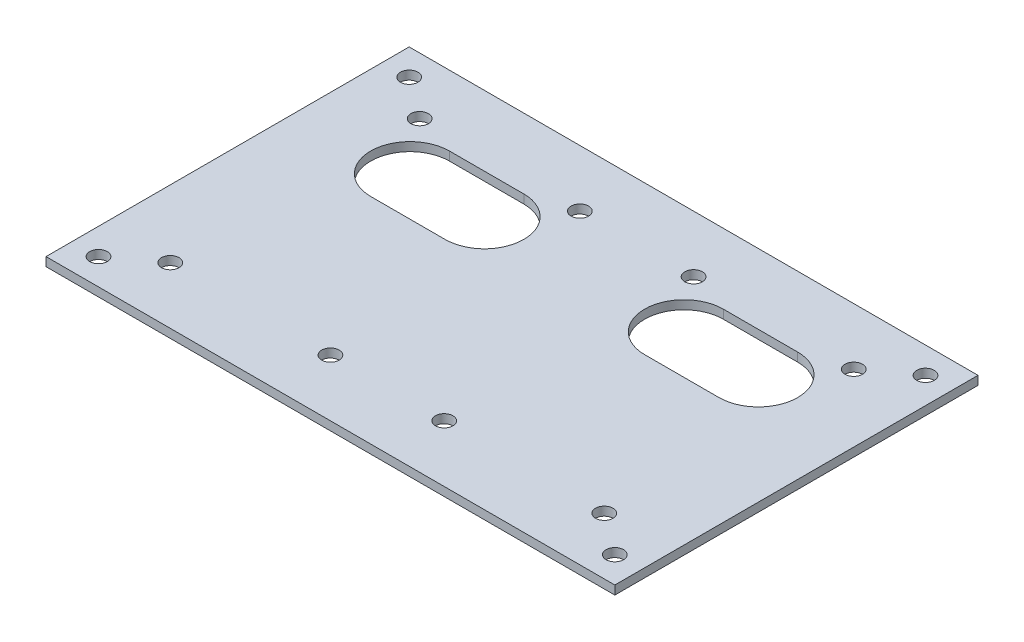
SolidWorks part; units mm, degrees
ref_plane "Front Plane" through (0, 0, 0) normal (0, 0, 1) x (1, 0, 0)
ref_plane "Top Plane" through (0, 0, 0) normal (0, 1, 0) x (1, 0, 0)
ref_plane "Right Plane" through (0, 0, 0) normal (1, 0, 0) x (0, 0, -1)
sketch "Sketch1" plane through (0, 0, 0) normal (0, 1, 0) x (1, 0, 0)
  line L0 (0, 53.99) -> (0, -62.5646) construction
  line L1 (10, 31.5) -> (52.6, 31.5) construction
  line L2 (10, 31.5) -> (10, -31.5) construction
  line L3 (10, -31.5) -> (52.6, -31.5) construction
  line L4 (52.6, 31.5) -> (52.6, -31.5) construction
  line L5 (10, 31.5) -> (52.6, -31.5) construction
  line L6 (10, -31.5) -> (52.6, 31.5) construction
  line L7 (13, 28.5) -> (49.6, 28.5) construction
  line L8 (13, 28.5) -> (13, -28.5) construction
  line L9 (13, -28.5) -> (49.6, -28.5) construction
  line L10 (49.6, 28.5) -> (49.6, -28.5) construction
  line L11 (13, 28.5) -> (49.6, -28.5) construction
  line L12 (13, -28.5) -> (49.6, 28.5) construction
  line L13 (-13, -28.5) -> (-49.6, 28.5) construction
  line L14 (-13, 28.5) -> (-49.6, -28.5) construction
  line L15 (-49.6, 28.5) -> (-49.6, -28.5) construction
  line L16 (-13, -28.5) -> (-49.6, -28.5) construction
  line L17 (-13, 28.5) -> (-13, -28.5) construction
  line L18 (-13, 28.5) -> (-49.6, 28.5) construction
  line L19 (-10, -31.5) -> (-52.6, 31.5) construction
  line L20 (-10, 31.5) -> (-52.6, -31.5) construction
  line L21 (-52.6, 31.5) -> (-52.6, -31.5) construction
  line L22 (-10, -31.5) -> (-52.6, -31.5) construction
  line L23 (-10, 31.5) -> (-10, -31.5) construction
  line L24 (-10, 31.5) -> (-52.6, 31.5) construction
  line L25 (-59, 35.5) -> (59, 35.5) construction
  line L26 (-65, 41.5) -> (65, 41.5)
  line L27 (-65, 41.5) -> (-65, -41.5)
  line L28 (-65, -41.5) -> (65, -41.5)
  line L29 (65, 41.5) -> (65, -41.5)
  line L30 (-65, 41.5) -> (65, -41.5) construction
  line L31 (-65, -41.5) -> (65, 41.5) construction
  line L32 (59, 35.5) -> (59, -35.5) construction
  line L33 (-59, -35.5) -> (59, -35.5) construction
  line L34 (-59, 35.5) -> (-59, -35.5) construction
  line L35 (31.3, 31.5) -> (31.3, -31.5) construction
  line L36 (22.8, 16.5) -> (39.8, 16.5) construction
  line L37 (22.8, 16.5) -> (39.8, 16.5) construction
  line L38 (22.8, 25.5) -> (39.8, 25.5)
  line L39 (22.8, 7.5) -> (39.8, 7.5)
  line L40 (-22.8, 16.5) -> (-39.8, 16.5) construction
  line L41 (-22.8, 25.5) -> (-39.8, 25.5)
  line L42 (-22.8, 7.5) -> (-39.8, 7.5)
  circle A0 centre (13, 28.5) radius 2
  circle A1 centre (49.6, 28.5) radius 2
  circle A2 centre (49.6, -28.5) radius 2
  circle A3 centre (13, -28.5) radius 2
  circle A4 centre (-13, -28.5) radius 2
  circle A5 centre (-49.6, -28.5) radius 2
  circle A6 centre (-49.6, 28.5) radius 2
  circle A7 centre (-13, 28.5) radius 2
  circle A8 centre (-59, 35.5) radius 2
  circle A9 centre (59, 35.5) radius 2
  circle A10 centre (59, -35.5) radius 2
  circle A11 centre (-59, -35.5) radius 2
  arc A12 (22.8, 25.5) -> (22.8, 7.5) centre (22.8, 16.5) ccw
  arc A13 (39.8, 7.5) -> (39.8, 25.5) centre (39.8, 16.5) ccw
  arc A14 (-22.8, 25.5) -> (-22.8, 7.5) centre (-22.8, 16.5) cw
  arc A15 (-39.8, 7.5) -> (-39.8, 25.5) centre (-39.8, 16.5) cw
  point P0 (31.3, 0)
  point P5 (31.3, 0)
  point P30 (-31.3, 0)
  point P31 (0, 0)
  point P43 (31.3, 16.5)
  point P46 (31.3, 0)
  point P49 (31.3, 16.5)
  point P54 (13.8, 16.5)
  point P57 (-31.3, 16.5)
  dimension "D5" = 4
  dimension "D10" = 4
  dimension "D1" = 42.6
  dimension "D2" = 63
  dimension "D3" = 3
  dimension "D4" = 3
  dimension "D6" = 10
  dimension "D7" = 130
  dimension "D8" = 83
  dimension "D11" = 17
  dimension "D12" = 15
  dimension "D13" = 9
  dimension "D9" = 6
extrude "Boss-Extrude1" add sketch "Sketch1" along normal blind 2
